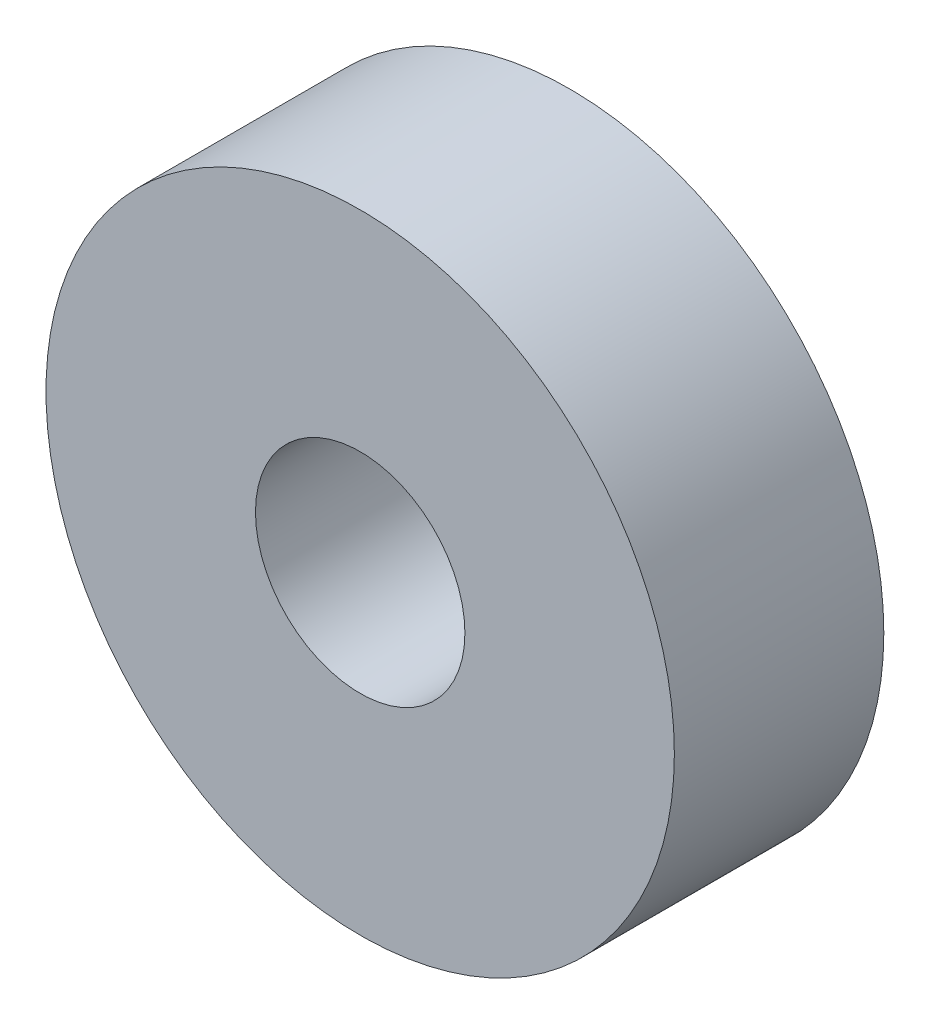
SolidWorks part; units mm, degrees
ref_plane "前视基准面" through (0, 0, 0) normal (0, 0, 1) x (1, 0, 0)
ref_plane "上视基准面" through (0, 0, 0) normal (0, 1, 0) x (1, 0, 0)
ref_plane "右视基准面" through (0, 0, 0) normal (1, 0, 0) x (0, 0, -1)
sketch "草图1" plane through (0, 0, 0) normal (0, 0, 1) x (1, 0, 0)
  circle A0 centre (0, 0) radius 6
  circle A1 centre (0, 0) radius 2
  dimension "D1" = 12
  dimension "D2" = 4
extrude "凸台-拉伸1" add sketch "草图1" along normal blind 4
